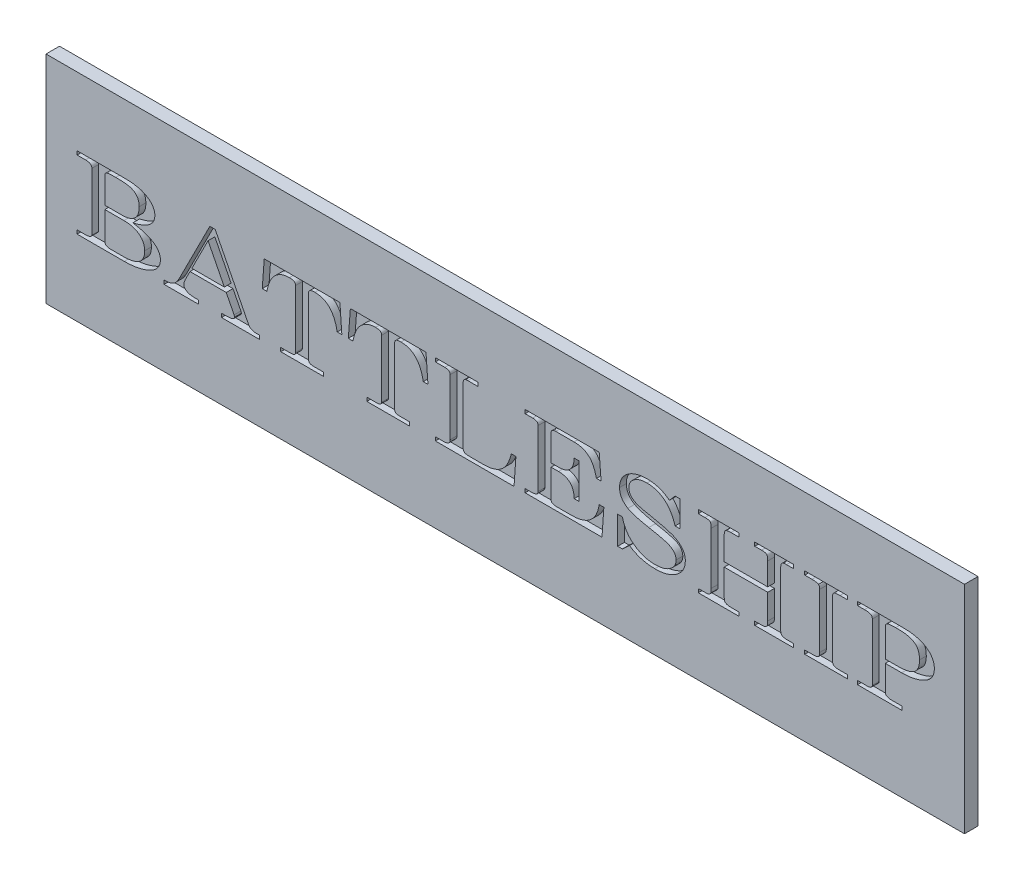
SolidWorks part; units mm, degrees
ref_plane "Front Plane" through (0, 0, 0) normal (0, 0, 1) x (1, 0, 0)
ref_plane "Top Plane" through (0, 0, 0) normal (0, 1, 0) x (1, 0, 0)
ref_plane "Right Plane" through (0, 0, 0) normal (1, 0, 0) x (0, 0, -1)
sketch "Sketch2" plane through (0, 0, 0) normal (0, 0, 1) x (1, 0, 0)
  line L1 (-107.95, 25.4) -> (107.95, 25.4)
  line L2 (-107.95, 25.4) -> (-107.95, -25.4)
  line L3 (-107.95, -25.4) -> (107.95, -25.4)
  line L4 (107.95, 25.4) -> (107.95, -25.4)
  line L5 (-107.95, 25.4) -> (107.95, -25.4) construction
  line L6 (-107.95, -25.4) -> (107.95, 25.4) construction
  point P0 (0, 0)
  point P9 (0, 0)
extrude "Boss-Extrude1" add sketch "Sketch2" along normal blind 3.175
sketch "Sketch4" plane through (0, 0, 3.175) normal (0, 0, 1) x (1, 0, 0)
  text T0 "BATTLESHIP" font "Century Schoolbook" height in points 65
extrude "Cut-Extrude1" cut sketch "Sketch4" against normal blind 1.5875
